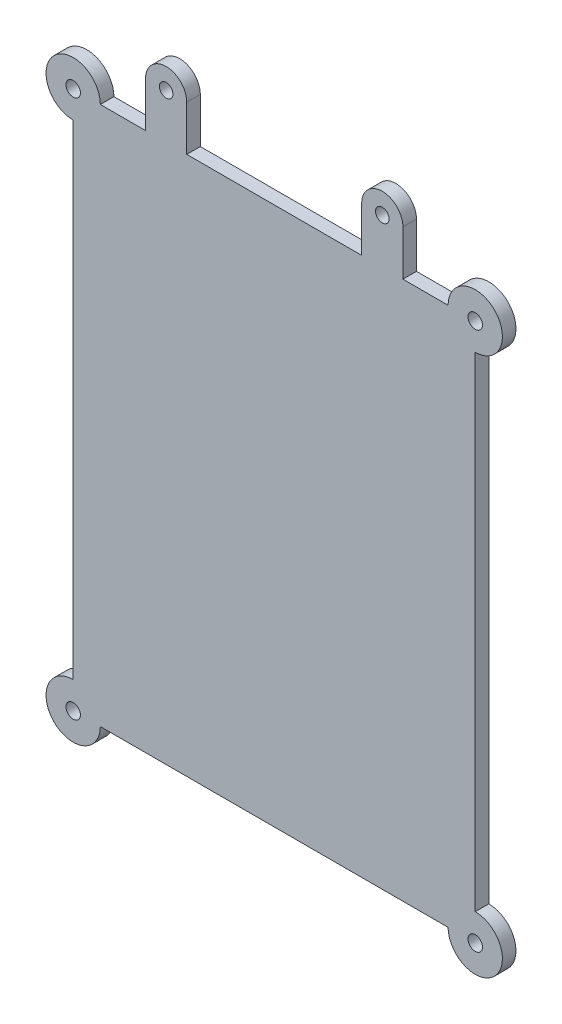
SolidWorks part; units mm, degrees
ref_plane "Front Plane" through (0, 0, 0) normal (0, 0, 1) x (1, 0, 0)
ref_plane "Top Plane" through (0, 0, 0) normal (0, 1, 0) x (1, 0, 0)
ref_plane "Right Plane" through (0, 0, 0) normal (1, 0, 0) x (0, 0, -1)
sketch "Sketch1" plane through (0, 0, 0) normal (0, 0, 1) x (1, 0, 0)
  line L0 (38.4589, -59.571) -> (-38.4589, -59.571) construction
  line L1 (-44.4589, -53.571) -> (-44.4589, 53.571) construction
  line L2 (-38.4589, 59.571) -> (38.4589, 59.571) construction
  line L3 (44.4589, 53.571) -> (44.4589, -53.571) construction
  line L4 (38.4589, -59.571) -> (-38.4589, -59.571)
  line L5 (-44.4589, -53.571) -> (-44.4589, 53.571)
  line L6 (-38.4589, 59.571) -> (38.4589, 59.571)
  line L7 (44.4589, 53.571) -> (44.4589, -53.571)
  arc A0 (-44.4589, -53.571) -> (-38.4589, -59.571) centre (-44.4589, -59.571) ccw construction
  arc A1 (-38.4589, 59.571) -> (-44.4589, 53.571) centre (-44.4589, 59.571) ccw construction
  arc A2 (44.4589, 53.571) -> (38.4589, 59.571) centre (44.4589, 59.571) ccw construction
  arc A3 (38.4589, -59.571) -> (44.4589, -53.571) centre (44.4589, -59.571) ccw construction
  arc A4 (-44.4589, -53.571) -> (-38.4589, -59.571) centre (-44.4589, -59.571) ccw
  arc A5 (-38.4589, 59.571) -> (-44.4589, 53.571) centre (-44.4589, 59.571) ccw
  arc A6 (44.4589, 53.571) -> (38.4589, 59.571) centre (44.4589, 59.571) ccw
  arc A7 (38.4589, -59.571) -> (44.4589, -53.571) centre (44.4589, -59.571) ccw
extrude "Boss-Extrude1" add sketch "Sketch1" along normal blind 3
sketch "Sketch2" plane through (0, 0, 3) normal (0, 0, 1) x (1, 0, 0)
  circle A0 centre (-44.4589, 59.571) radius 1.6
  circle A1 centre (44.4589, 59.571) radius 1.6
  circle A2 centre (44.4589, -59.571) radius 1.6
  circle A3 centre (-44.4589, -59.571) radius 1.6
  dimension "D1" = 3.2
extrude "Cut-Extrude1" cut sketch "Sketch2" against normal blind 10
sketch "Sketch3" plane through (0, 0, 3) normal (0, 0, 1) x (1, 0, 0)
  line L0 (19.3448, 59.571) -> (28.4589, 59.571)
  line L1 (38.4589, 59.571) -> (-38.4589, 59.571) construction
  line L2 (19.3448, 59.571) -> (19.3448, 69.571)
  line L3 (28.4589, 59.571) -> (28.4589, 69.571)
  line L5 (-19.3448, 59.571) -> (-28.4589, 59.571)
  line L6 (-28.4589, 59.571) -> (-28.4589, 69.571)
  line L7 (-19.3448, 59.571) -> (-19.3448, 69.571)
  arc A0 (28.4589, 69.571) -> (19.3448, 69.571) centre (23.9018, 69.571) ccw
  circle A1 centre (23.9018, 69.571) radius 1.5
  circle A2 centre (-23.9018, 69.571) radius 1.5
  arc A3 (-28.4589, 69.571) -> (-19.3448, 69.571) centre (-23.9018, 69.571) cw
  point P5 (0, 59.571)
  dimension "D1" = 3
  dimension "D2" = 10
  dimension "D3" = 10
extrude "Boss-Extrude4" add sketch "Sketch3" against normal blind 3
